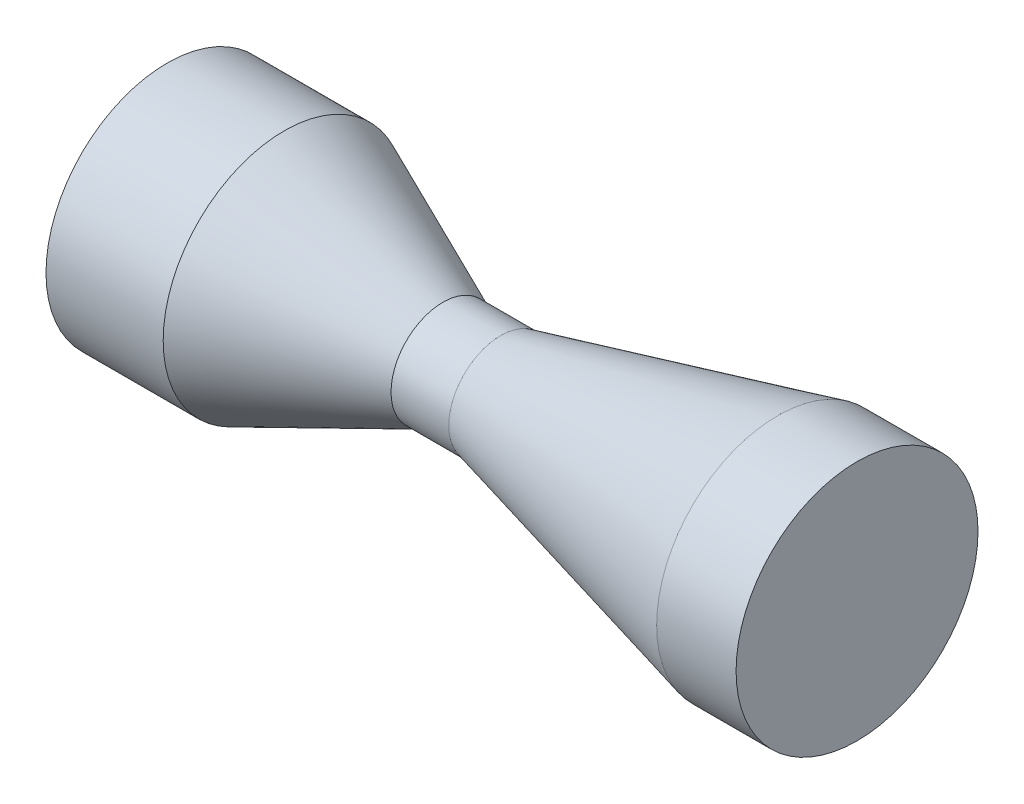
SolidWorks part; units mm, degrees
ref_plane "Front Plane" through (0, 0, 0) normal (0, 0, 1) x (1, 0, 0)
ref_plane "Top Plane" through (0, 0, 0) normal (0, 1, 0) x (1, 0, 0)
ref_plane "Right Plane" through (0, 0, 0) normal (1, 0, 0) x (0, 0, -1)
sketch "Sketch1" plane through (0, 0, 0) normal (0, 0, 1) x (1, 0, 0)
  line L0 (-43.0232, 0) -> (128.8214, 0) construction
  line L1 (-56.4949, 25) -> (-26.7253, 25)
  line L2 (-26.7253, 25) -> (19.1004, 5)
  line L3 (19.1004, 5) -> (39.1004, 5)
  line L4 (39.1004, 5) -> (119.1004, 24.9462)
  line L5 (119.1004, 24.9462) -> (138.8214, 24.9462)
  dimension "D1" = 50
  dimension "D2" = 25
  dimension "D3" = 5
  dimension "D4" = 14
  dimension "D5" = 80
  dimension "D6" = 20
  dimension "D7" = 24.9462
  dimension "D8" = 23.578
revolve "Revolve-Thin1" add sketch "Sketch1" angle 360 about L0 wall 10
fillet "Fillet1" radius 10 2 edges at (19.1004, 0, 5) (39.1004, 0, 5)
sketch "Sketch2" plane through (-56.4949, 0, 0) normal (-1, 0, 0) x (0, 0, 1)
  circle A0 centre (0, 0) radius 35 construction
  circle A1 centre (0, 0) radius 35
extrude "Boss-Extrude1" add sketch "Sketch2" along normal blind 2
sketch "Sketch3" plane through (138.8214, 0, 0) normal (1, 0, 0) x (0, 0, -1)
  circle A0 centre (0, 0) radius 34.9462 construction
  circle A1 centre (0, 0) radius 34.9462
extrude "Boss-Extrude2" add sketch "Sketch3" along normal blind 2
sketch "Sketch4" plane through (0, 0, 0) normal (0, 0, 1) x (1, 0, 0)
  point P0 (30.4274, 0)
  point P1 (100.5825, 13.0744)
  point P2 (102.4958, -15.4129)
  point P3 (-36.5388, -17.5388)
  point P4 (-38.027, 15.4129)
